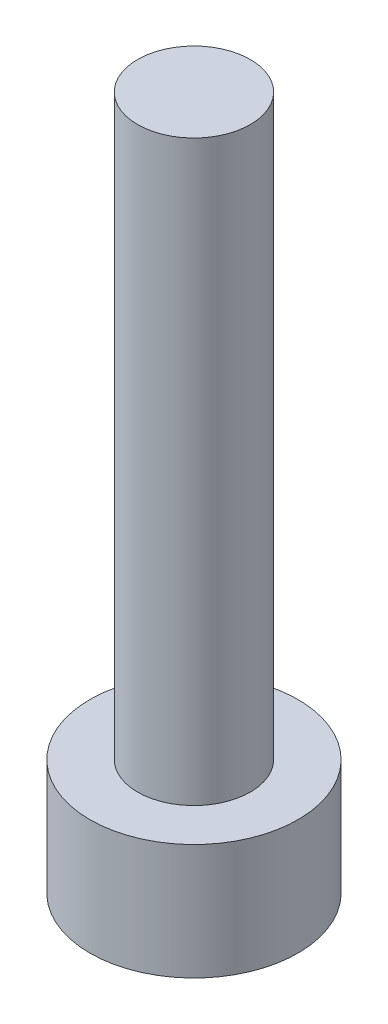
SolidWorks part; units mm, degrees
material "Cast Alloy Steel"
ref_plane "Front Plane" through (0, 0, 0) normal (0, 0, 1) x (1, 0, 0)
ref_plane "Top Plane" through (0, 0, 0) normal (0, 1, 0) x (1, 0, 0)
ref_plane "Right Plane" through (0, 0, 0) normal (1, 0, 0) x (0, 0, -1)
sketch "Sketch1" plane through (0, 0, 0) normal (0, 1, 0) x (1, 0, 0)
  circle A0 centre (0, 0) radius 3.6
  dimension "D1" = 7.2
extrude "Boss-Extrude1" add sketch "Sketch1" along normal blind 4
sketch "Sketch2" plane through (0, 4, 0) normal (0, 1, 0) x (1, 0, 0)
  circle A0 centre (0, 0) radius 1.95
  dimension "D1" = 3.9
extrude "Boss-Extrude2" add sketch "Sketch2" along normal blind 20
sketch "Sketch3" plane through (0, 0, 0) normal (0, -1, 0) x (1, 0, 0)
  line L1 (0, 2.0227) -> (-1.7517, 1.0113)
  line L2 (-1.7517, 1.0113) -> (-1.7517, -1.0113)
  line L3 (-1.7517, -1.0113) -> (0, -2.0227)
  line L4 (0, -2.0227) -> (1.7517, -1.0113)
  line L5 (1.7517, -1.0113) -> (1.7517, 1.0113)
  line L6 (1.7517, 1.0113) -> (0, 2.0227)
  circle A0 centre (0, 0) radius 1.7517 construction
extrude "Cut-Extrude1" cut sketch "Sketch3" against normal blind 2
